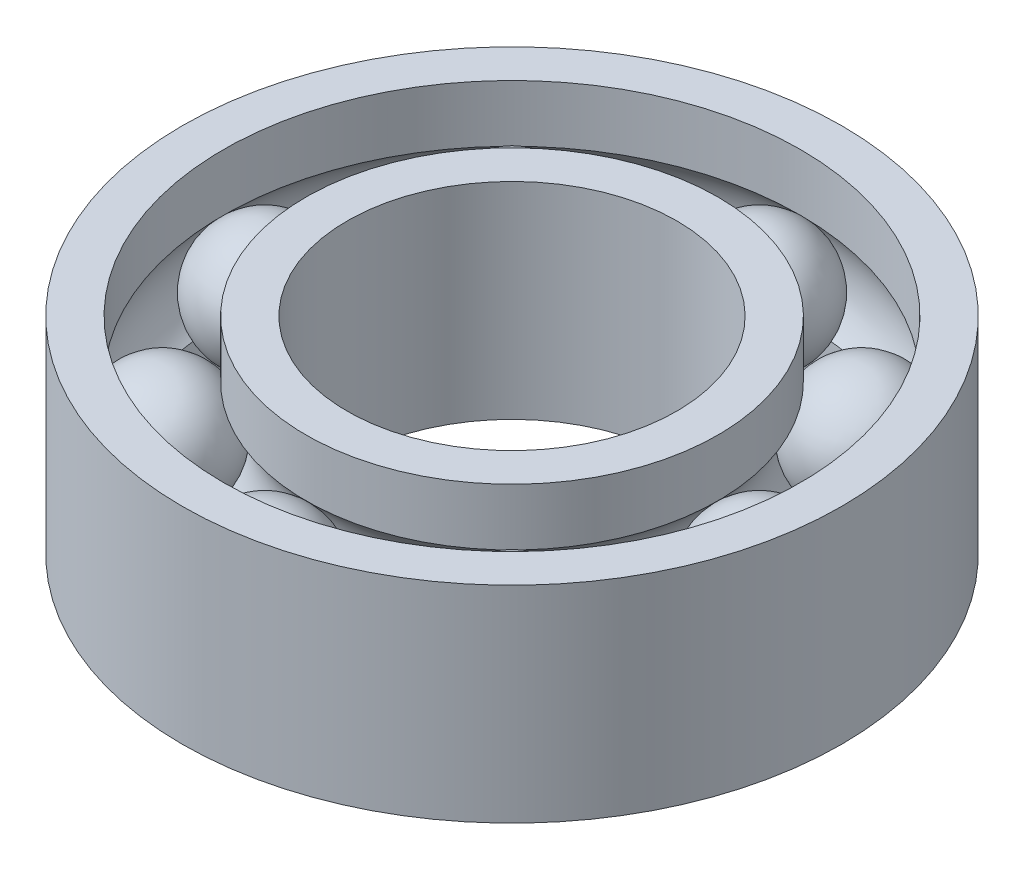
SolidWorks part; units mm, degrees
ref_plane "Front Plane" through (0, 0, 0) normal (0, 0, 1) x (1, 0, 0)
ref_plane "Top Plane" through (0, 0, 0) normal (0, 1, 0) x (1, 0, 0)
ref_plane "Right Plane" through (0, 0, 0) normal (1, 0, 0) x (0, 0, -1)
sketch "Sketch1" plane through (0, 0, 0) normal (0, 0, 1) x (1, 0, 0)
  line L0 (-6, 3.75) -> (-7.5, 1.875) construction
  line L1 (-7.5, 3.75) -> (-6, 3.75)
  line L2 (-7.5, 3.75) -> (-7.5, 1.6771)
  line L3 (-7.5, -3.75) -> (-6, -3.75)
  line L4 (-6, 3.75) -> (-6, -3.75)
  line L5 (-7.5, 3.75) -> (-6, -3.75) construction
  line L6 (-7.5, -3.75) -> (-6, 3.75) construction
  line L7 (-12, 3.75) -> (-10.5, 3.75)
  line L8 (-12, 3.75) -> (-12, -3.75)
  line L9 (-12, -3.75) -> (-10.5, -3.75)
  line L10 (-10.5, 3.75) -> (-10.5, 1.6771)
  line L11 (-12, 3.75) -> (-10.5, -3.75) construction
  line L12 (-12, -3.75) -> (-10.5, 3.75) construction
  line L13 (-10.5, -1.875) -> (-12, -3.75) construction
  line L14 (-10.5, -1.6771) -> (-10.5, -3.75)
  line L15 (-7.5, -1.6771) -> (-7.5, -3.75)
  arc A0 (-7.5, -1.6771) -> (-7.5, 1.6771) centre (-9, 0) ccw
  arc A1 (-10.5, 1.6771) -> (-10.5, -1.6771) centre (-9, 0) ccw
  point P0 (-6.75, 0)
  point P7 (-11.25, 0)
  point P14 (0, 0)
  dimension "D7" = 4.5
  dimension "D1" = 6
  dimension "D2" = 1.5
  dimension "D3" = 7.5
  dimension "D4" = 12
  dimension "D5" = 1.5
  dimension "D6" = 7.5
sketch "Sketch4" plane through (0, 0, 0) normal (0, 0, 1) x (1, 0, 0)
  line L0 (-9, 2.25) -> (-9, -2.25)
  arc A0 (-9, 2.25) -> (-9, -2.25) centre (-9, 0) ccw
  dimension "D1" = 2.25
revolve "Revolve4" add sketch "Sketch4" angle 360 about L0
ref_axis "Axis3" through (0, -4.125, 0) along (0, 1, 0)
revolve "Revolve5" add sketch "Sketch1" angle 360 about axis through (0, -4.125, 0) along (0, 1, 0)
pattern_circular "CirPattern2" count 8 over 360 about axis through (0, 0, 0) along (0, 1, 0) of bodies 112
